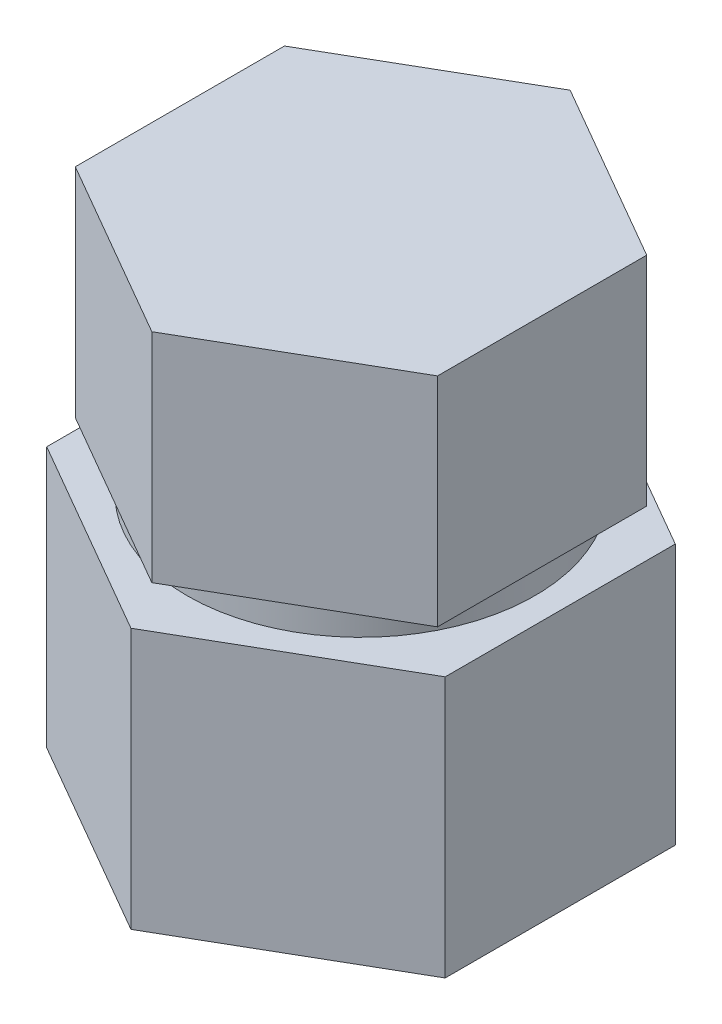
SolidWorks part; units mm, degrees
ref_plane "前视基准面" through (0, 0, 0) normal (0, 0, 1) x (1, 0, 0)
ref_plane "上视基准面" through (0, 0, 0) normal (0, 1, 0) x (1, 0, 0)
ref_plane "右视基准面" through (0, 0, 0) normal (1, 0, 0) x (0, 0, -1)
other "Configuration Table"
sketch "草图2" plane through (0, 0, 0) normal (0, 1, 0) x (1, 0, 0)
  line L1 (0, -2.8868) -> (2.5, -1.4434)
  line L2 (2.5, -1.4434) -> (2.5, 1.4434)
  line L3 (2.5, 1.4434) -> (0, 2.8868)
  line L4 (0, 2.8868) -> (-2.5, 1.4434)
  line L5 (-2.5, 1.4434) -> (-2.5, -1.4434)
  line L6 (-2.5, -1.4434) -> (0, -2.8868)
  circle A0 centre (0, 0) radius 2.5 construction
  dimension "D1" = 5
extrude "凸台-拉伸1" add sketch "草图2" against normal blind 3
sketch "草图3" plane through (0, -3, 0) normal (0, -1, 0) x (1, 0, 0)
  circle A0 centre (0, 0) radius 2.4
  dimension "D1" = 4.8
extrude "凸台-拉伸2" add sketch "草图3" along normal blind 0.4
sketch "草图4" plane through (0, -3.4, 0) normal (0, -1, 0) x (1, 0, 0)
  line L1 (0, -3.1754) -> (2.75, -1.5877)
  line L2 (2.75, -1.5877) -> (2.75, 1.5877)
  line L3 (2.75, 1.5877) -> (0, 3.1754)
  line L4 (0, 3.1754) -> (-2.75, 1.5877)
  line L5 (-2.75, 1.5877) -> (-2.75, -1.5877)
  line L6 (-2.75, -1.5877) -> (0, -3.1754)
  circle A0 centre (0, 0) radius 2.75 construction
  dimension "D1" = 5.5
extrude "凸台-拉伸3" add sketch "草图4" along normal blind 3.6
